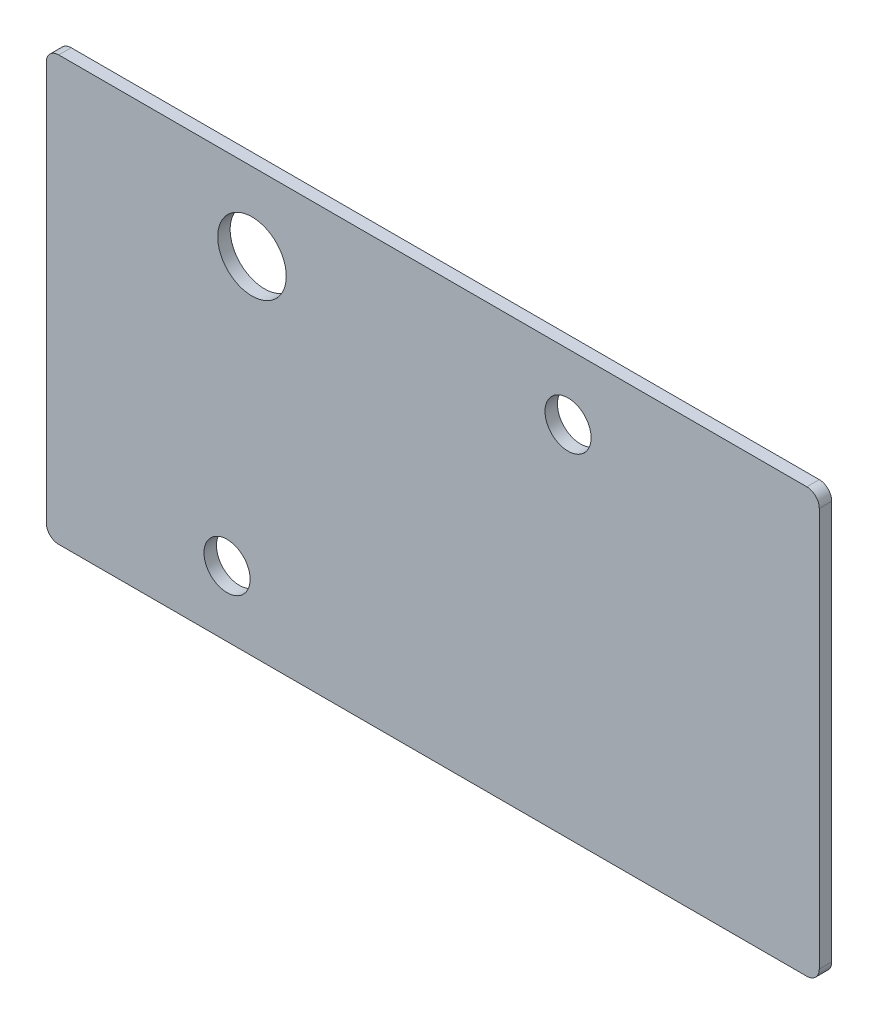
SolidWorks part; units mm, degrees
ref_plane "Alzado" through (0, 0, 0) normal (0, 0, 1) x (1, 0, 0)
ref_plane "Planta" through (0, 0, 0) normal (0, 1, 0) x (1, 0, 0)
ref_plane "Vista lateral" through (0, 0, 0) normal (1, 0, 0) x (0, 0, -1)
sketch "Croquis1" plane through (0, 0, 0) normal (0, 0, 1) x (1, 0, 0)
  line L0 (-5, 31.75) -> (55, 31.75)
  line L1 (0, 0) -> (40, 0) construction
  line L2 (0, 0) -> (0, 29.5) construction
  line L3 (0, 29.5) -> (40, 29.5) construction
  line L4 (40, 0) -> (40, 29.5) construction
  line L5 (56, -1.25) -> (56, 30.75)
  line L6 (-5, -2.25) -> (55, -2.25)
  line L7 (-6, -1.25) -> (-6, 30.75)
  circle A0 centre (35.85, 26.5) radius 1.85
  circle A1 centre (8.5, 3) radius 1.85
  arc A2 (-6, -1.25) -> (-5, -2.25) centre (-5, -1.25) ccw
  arc A3 (55, -2.25) -> (56, -1.25) centre (55, -1.25) ccw
  arc A4 (56, 30.75) -> (55, 31.75) centre (55, 30.75) ccw
  arc A5 (-5, 31.75) -> (-6, 30.75) centre (-5, 30.75) ccw
  dimension "D3" = 3.7
  dimension "D4" = 3
  dimension "D5" = 4.15
  dimension "D6" = 8.5
  dimension "D7" = 3
  dimension "D9" = 1
  dimension "D1" = 40
  dimension "D2" = 29.5
  dimension "D8" = 2.25
  dimension "D10" = 6
  dimension "D11" = 2.25
  dimension "D12" = 16
  dimension "D13" = 62
  dimension "D14" = 34
extrude "Saliente-Extruir1" add sketch "Croquis1" along normal blind 1
sketch "Croquis2" plane through (0, 0, 1) normal (0, 0, 1) x (1, 0, 0)
  line L0 (0, 29.5) -> (40, 29.5) construction
  line L1 (0, 0) -> (0, 29.5) construction
  circle A0 centre (10.5, 25.5) radius 2.75
  dimension "D1" = 5.5
  dimension "D2" = 4
  dimension "D3" = 10.5
extrude "Cortar-Extruir1" cut sketch "Croquis2" against normal through all
